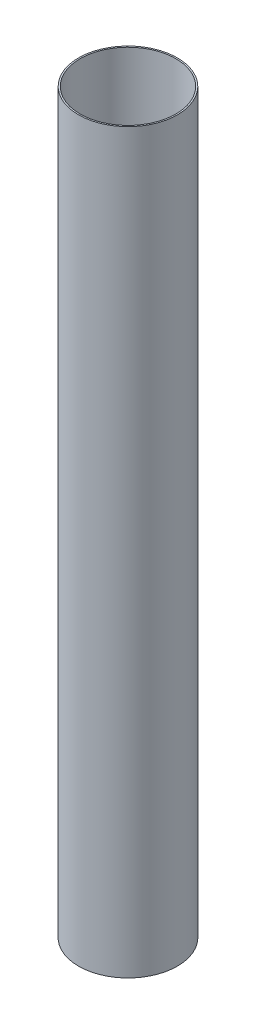
SolidWorks part; units mm, degrees
ref_plane "Front Plane" through (0, 0, 0) normal (0, 0, 1) x (1, 0, 0)
ref_plane "Top Plane" through (0, 0, 0) normal (0, 1, 0) x (1, 0, 0)
ref_plane "Right Plane" through (0, 0, 0) normal (1, 0, 0) x (0, 0, -1)
sketch "Sketch1" plane through (0, 0, 0) normal (0, 1, 0) x (1, 0, 0)
  circle A0 centre (0, 0) radius 65
  circle A1 centre (0, 0) radius 67
  dimension "D1" = 130
  dimension "D2" = 134
extrude "Boss-Extrude1" add sketch "Sketch1" along normal mid plane 1000
